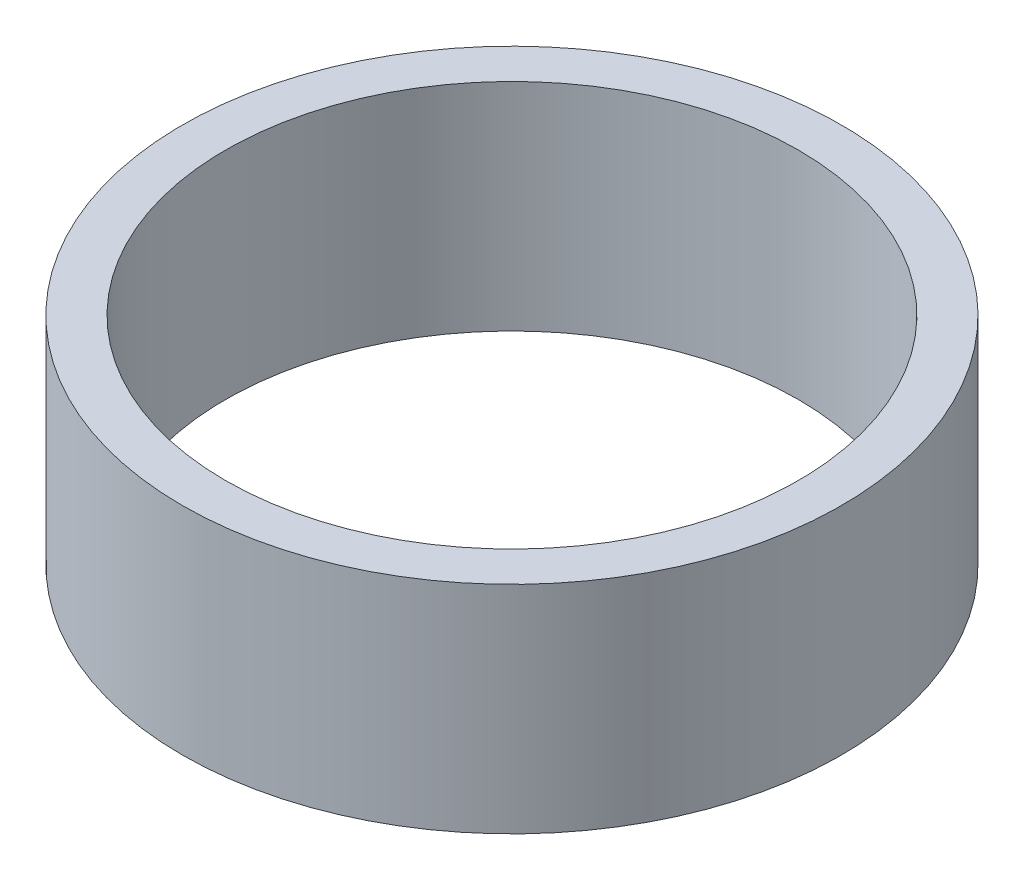
SolidWorks part; units mm, degrees
material "ｽﾃﾝﾚｽ鋼(ｸﾛﾑ)"
ref_plane "正面" through (0, 0, 0) normal (0, 0, 1) x (1, 0, 0)
ref_plane "平面" through (0, 0, 0) normal (0, 1, 0) x (1, 0, 0)
ref_plane "右側面" through (0, 0, 0) normal (1, 0, 0) x (0, 0, -1)
sketch "ｽｹｯﾁ2" plane through (0, 0, 0) normal (0, 1, 0) x (1, 0, 0)
  circle A0 centre (0, 0) radius 15.25
  circle A1 centre (0, 0) radius 13.25
  dimension "D1" = 30.5
  dimension "D2" = 26.5
extrude "ﾎﾞｽ - 押し出し1" add sketch "ｽｹｯﾁ2" along normal blind 10
